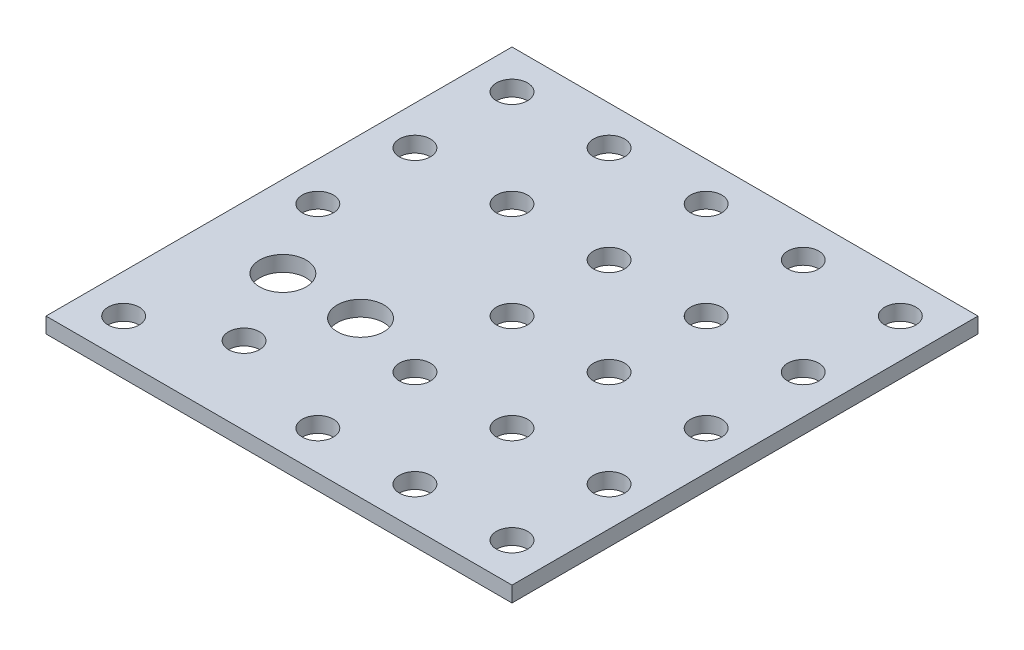
SolidWorks part; units mm, degrees
ref_plane "Plan de face" through (0, 0, 0) normal (0, 0, 1) x (1, 0, 0)
ref_plane "Plan de dessus" through (0, 0, 0) normal (0, 1, 0) x (1, 0, 0)
ref_plane "Plan de droite" through (0, 0, 0) normal (1, 0, 0) x (0, 0, -1)
sketch "Esquisse1" plane through (0, 0, 0) normal (0, 1, 0) x (1, 0, 0)
  line L0 (0, 0) -> (60, 0)
  line L1 (0, 0) -> (0, 60)
  line L2 (60, 0) -> (60, 60)
  line L3 (0, 60) -> (60, 60)
extrude "Boss.-Extru.1" add sketch "Esquisse1" along normal blind 2
sketch "Esquisse4" plane through (0, 2, 0) normal (0, 1, 0) x (1, 0, 0)
  circle A0 centre (10.5, 20) radius 3
  circle A1 centre (20.5, 20) radius 3
  circle A2 centre (15.5, 10) radius 2
extrude "Enlèv. mat.-Extru.1" cut sketch "Esquisse4" against normal blind 10
sketch "Esquisse5" plane through (0, 2, 0) normal (0, 1, 0) x (1, 0, 0)
  circle A0 centre (5, 5) radius 2
  circle A1 centre (55, 5) radius 2
  circle A2 centre (55, 55) radius 2
  circle A3 centre (5, 55) radius 2
  circle A4 centre (30, 55) radius 2
  circle A5 centre (30, 5) radius 2
  circle A6 centre (30, 30) radius 2
  circle A7 centre (55, 30) radius 2
  circle A8 centre (5, 30) radius 2
extrude "Enlèv. mat.-Extru.2" cut sketch "Esquisse5" against normal blind 10
sketch "Esquisse12" plane through (0, 2, 0) normal (0, 1, 0) x (1, 0, 0)
  circle A0 centre (17.5, 55) radius 2
  circle A1 centre (42.5, 55) radius 2
  circle A2 centre (42.5, 42.5) radius 2
  circle A3 centre (17.5, 42.5) radius 2
  circle A4 centre (42.5, 17.5) radius 2
  circle A5 centre (55, 17.5) radius 2
  circle A6 centre (55, 42.5) radius 2
  circle A7 centre (42.5, 5) radius 2
  circle A8 centre (42.5, 30) radius 2
  circle A9 centre (5, 42.5) radius 2
  circle A10 centre (30, 42.5) radius 2
  circle A11 centre (30, 17.5) radius 2
extrude "Enlèv. mat.-Extru.5" cut sketch "Esquisse12" against normal blind 2
